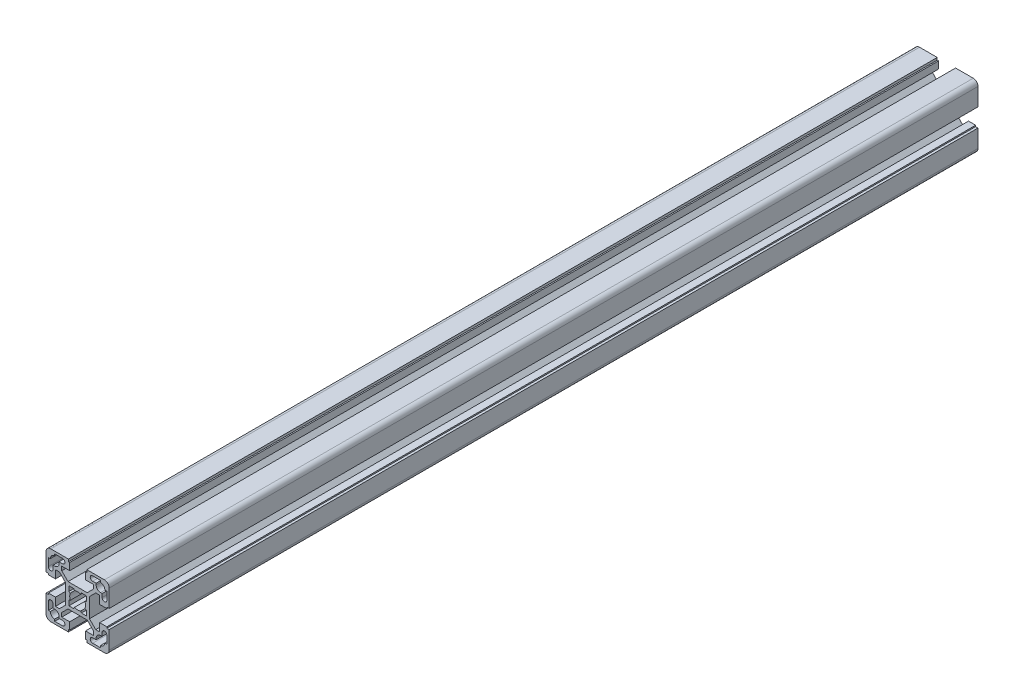
SolidWorks part; units mm, degrees
material "6061 Alloy"
ref_plane "Front Plane" through (0, 0, 0) normal (0, 0, 1) x (1, 0, 0)
ref_plane "Top Plane" through (0, 0, 0) normal (0, 1, 0) x (1, 0, 0)
ref_plane "Right Plane" through (0, 0, 0) normal (1, 0, 0) x (0, 0, -1)
sketch "Sketch1" plane through (0, 0, 0) normal (0, 0, 1) x (1, 0, 0)
  line L0 (5.8, -20) -> (17, -20)
  line L1 (14, -10.05) -> (11.4642, -10.05)
  line L2 (0, -21.1722) -> (0, 18.817) construction
  line L3 (0, 21.1722) -> (0, -18.817) construction
  line L4 (14.5, -18.5) -> (9.5, -18.5)
  line L5 (18.5, 5) -> (14, 5)
  line L6 (6.0858, -7.5) -> (10.05, -11.4642)
  line L7 (20, 5.8) -> (18.5, 5.8)
  line L8 (14, 5) -> (14, 10.05)
  line L9 (18.5, 5.8) -> (18.5, 5)
  line L10 (18.5, 14.5) -> (17.25, 14.5)
  line L11 (14.5, 11.75) -> (15.5, 11.75)
  line L12 (14.5, 17.25) -> (14.5, 18.5)
  line L13 (18.5, 9.5) -> (18.5, 14.5)
  line L14 (15.5, 11.75) -> (15.5, 9.5)
  line L15 (20, 17) -> (20, 5.8)
  line L16 (5.5, 5.5) -> (2.3979, 5.5)
  line L17 (2.3979, 5.5) -> (1.9983, 4.5833)
  line L18 (5.5, 2.3979) -> (5.5, 5.5)
  line L19 (4.5833, 1.9983) -> (5.5, 2.3979)
  line L20 (5, -14) -> (5, -18.5)
  line L21 (11.4642, 10.05) -> (7.5, 6.0858)
  line L22 (-6.0858, 7.5) -> (6.0858, 7.5)
  line L23 (11.75, 15.5) -> (11.75, 14.5)
  line L24 (5, -18.5) -> (5.8, -18.5)
  line L25 (5.8, -18.5) -> (5.8, -20)
  line L26 (10.05, -11.4642) -> (10.05, -14)
  line L27 (10.05, -14) -> (5, -14)
  line L28 (9.5, -15.5) -> (11.75, -15.5)
  line L29 (11.75, -15.5) -> (11.75, -14.5)
  line L30 (9.5, 15.5) -> (11.75, 15.5)
  line L31 (10.05, 14) -> (5, 14)
  line L32 (10.05, 11.4642) -> (10.05, 14)
  line L33 (5.8, 18.5) -> (5.8, 20)
  line L34 (5, 18.5) -> (5.8, 18.5)
  line L35 (7.5, -6.0858) -> (7.5, 6.0858)
  line L36 (5, 14) -> (5, 18.5)
  line L37 (6.0858, 7.5) -> (10.05, 11.4642)
  line L38 (14.5, 18.5) -> (9.5, 18.5)
  line L39 (14, 10.05) -> (11.4642, 10.05)
  line L40 (5.8, 20) -> (17, 20)
  line L41 (-18.5, -5) -> (-14, -5)
  line L42 (-6.0858, -7.5) -> (6.0858, -7.5)
  line L43 (11.4642, -10.05) -> (7.5, -6.0858)
  line L44 (-20, -5.8) -> (-18.5, -5.8)
  line L45 (-14, -5) -> (-14, -10.05)
  line L46 (-18.5, -5.8) -> (-18.5, -5)
  line L47 (-18.5, -14.5) -> (-17.25, -14.5)
  line L48 (4.5833, -1.9983) -> (5.5, -2.3979)
  line L49 (5.5, -2.3979) -> (5.5, -5.5)
  line L50 (2.3979, -5.5) -> (1.9983, -4.5833)
  line L51 (5.5, -5.5) -> (2.3979, -5.5)
  line L52 (-14.5, -11.75) -> (-15.5, -11.75)
  line L53 (-14.5, -17.25) -> (-14.5, -18.5)
  line L54 (-18.5, -9.5) -> (-18.5, -14.5)
  line L55 (-15.5, -11.75) -> (-15.5, -9.5)
  line L56 (-20, -17) -> (-20, -5.8)
  line L57 (-5.5, -5.5) -> (-2.3979, -5.5)
  line L58 (-2.3979, -5.5) -> (-1.9983, -4.5833)
  line L59 (-5.5, -2.3979) -> (-5.5, -5.5)
  line L60 (-4.5833, -1.9983) -> (-5.5, -2.3979)
  line L61 (-11.4642, -10.05) -> (-7.5, -6.0858)
  line L62 (-5.8, 20) -> (-17, 20)
  line L63 (-14, 10.05) -> (-11.4642, 10.05)
  line L64 (-14.5, 18.5) -> (-9.5, 18.5)
  line L65 (-6.0858, 7.5) -> (-10.05, 11.4642)
  line L66 (-5, 14) -> (-5, 18.5)
  line L67 (-7.5, -6.0858) -> (-7.5, 6.0858)
  line L68 (-5, 18.5) -> (-5.8, 18.5)
  line L69 (-5.8, 18.5) -> (-5.8, 20)
  line L70 (-10.05, 11.4642) -> (-10.05, 14)
  line L71 (-10.05, 14) -> (-5, 14)
  line L72 (-9.5, 15.5) -> (-11.75, 15.5)
  line L73 (-11.75, -15.5) -> (-11.75, -14.5)
  line L74 (-9.5, -15.5) -> (-11.75, -15.5)
  line L75 (-10.05, -14) -> (-5, -14)
  line L76 (-10.05, -11.4642) -> (-10.05, -14)
  line L77 (-5.8, -18.5) -> (-5.8, -20)
  line L78 (-5, -18.5) -> (-5.8, -18.5)
  line L79 (-11.75, 15.5) -> (-11.75, 14.5)
  line L80 (-11.4642, 10.05) -> (-7.5, 6.0858)
  line L81 (-5, -14) -> (-5, -18.5)
  line L82 (-4.5833, 1.9983) -> (-5.5, 2.3979)
  line L83 (-5.5, 2.3979) -> (-5.5, 5.5)
  line L84 (-2.3979, 5.5) -> (-1.9983, 4.5833)
  line L85 (-5.5, 5.5) -> (-2.3979, 5.5)
  line L86 (-20, 17) -> (-20, 5.8)
  line L87 (-15.5, 11.75) -> (-15.5, 9.5)
  line L88 (20, -17) -> (20, -5.8)
  line L89 (15.5, -11.75) -> (15.5, -9.5)
  line L90 (18.5, -9.5) -> (18.5, -14.5)
  line L91 (14.5, -17.25) -> (14.5, -18.5)
  line L92 (14.5, -11.75) -> (15.5, -11.75)
  line L93 (18.5, -14.5) -> (17.25, -14.5)
  line L94 (-18.5, 9.5) -> (-18.5, 14.5)
  line L95 (-14.5, 17.25) -> (-14.5, 18.5)
  line L96 (18.5, -5.8) -> (18.5, -5)
  line L97 (14, -5) -> (14, -10.05)
  line L98 (20, -5.8) -> (18.5, -5.8)
  line L99 (18.5, -5) -> (14, -5)
  line L100 (-14.5, 11.75) -> (-15.5, 11.75)
  line L101 (-18.5, 14.5) -> (-17.25, 14.5)
  line L102 (-18.5, 5.8) -> (-18.5, 5)
  line L103 (-14, 5) -> (-14, 10.05)
  line L104 (-20, 5.8) -> (-18.5, 5.8)
  line L105 (-6.0858, -7.5) -> (-10.05, -11.4642)
  line L106 (-18.5, 5) -> (-14, 5)
  line L107 (-14.5, -18.5) -> (-9.5, -18.5)
  line L108 (-20, 0) -> (20.788, 0) construction
  line L109 (-14, -10.05) -> (-11.4642, -10.05)
  line L110 (-5.8, -20) -> (-17, -20)
  arc A0 (14.5, -11.75) -> (11.75, -14.5) centre (14.5, -14.5) ccw
  arc A1 (18.5, 9.5) -> (15.5, 9.5) centre (17, 9.5) cw
  arc A2 (14.5, 17.25) -> (17.25, 14.5) centre (14.5, 14.5) cw
  arc A3 (17, 20) -> (20, 17) centre (17, 17) cw
  arc A4 (-1.9983, 4.5833) -> (1.9983, 4.5833) centre (0, 0) cw
  arc A5 (9.5, 15.5) -> (9.5, 18.5) centre (9.5, 17) cw
  arc A6 (9.5, -15.5) -> (9.5, -18.5) centre (9.5, -17) ccw
  arc A7 (14.5, 11.75) -> (11.75, 14.5) centre (14.5, 14.5) cw
  arc A8 (4.5833, -1.9983) -> (4.5833, 1.9983) centre (0, 0) ccw
  arc A9 (-18.5, -9.5) -> (-15.5, -9.5) centre (-17, -9.5) cw
  arc A10 (-14.5, -17.25) -> (-17.25, -14.5) centre (-14.5, -14.5) cw
  arc A11 (-1.9983, -4.5833) -> (1.9983, -4.5833) centre (0, 0) ccw
  arc A12 (-17, -20) -> (-20, -17) centre (-17, -17) cw
  arc A13 (-4.5833, -1.9983) -> (-4.5833, 1.9983) centre (0, 0) cw
  arc A14 (-14.5, 11.75) -> (-11.75, 14.5) centre (-14.5, 14.5) ccw
  arc A15 (-9.5, -15.5) -> (-9.5, -18.5) centre (-9.5, -17) cw
  arc A16 (-9.5, 15.5) -> (-9.5, 18.5) centre (-9.5, 17) ccw
  arc A17 (-17, 20) -> (-20, 17) centre (-17, 17) ccw
  arc A18 (17, -20) -> (20, -17) centre (17, -17) ccw
  arc A19 (14.5, -17.25) -> (17.25, -14.5) centre (14.5, -14.5) ccw
  arc A20 (18.5, -9.5) -> (15.5, -9.5) centre (17, -9.5) ccw
  arc A21 (-14.5, 17.25) -> (-17.25, 14.5) centre (-14.5, 14.5) ccw
  arc A22 (-18.5, 9.5) -> (-15.5, 9.5) centre (-17, 9.5) ccw
  arc A23 (-14.5, -11.75) -> (-11.75, -14.5) centre (-14.5, -14.5) cw
  point P55 (7.5, 0)
  point P101 (-7.5, 0)
  point P116 (0, -7.5)
  point P149 (0, 7.5)
extrude "Extrude1" add sketch "Sketch1" along normal mid plane 550
hole_wizard "M12 Tapped Hole1" positions "3DSketch2" profile "Sketch3" tap size "M12" standard "ISO"
sketch3d "3DSketch2"
  line L0 (-20, 17, 0) -> (-20, 5.8, 0) construction
  line L1 (-5.8, 20, 0) -> (-17, 20, 0) construction
  line L2 (-5.8, 20, 200) -> (-17, 20, 200) construction
  line L3 (-20, 17, 200) -> (-20, 5.8, 200) construction
  point P0 (0, 0, 200)
  point P2 (0, 0, 0)
  dimension "D1" = 20
  dimension "D2" = 20
  dimension "D3" = 20
  dimension "D4" = 20
sketch "Sketch3" plane through (0, 0, 200) normal (1, 0, 0) x (0, -1, 0)
  line L0 (0, 0) -> (0, 35.8144)
  line L1 (0, 35.8144) -> (5.1, 32.75)
  line L2 (5.1, 32.75) -> (5.1, 0.925)
  line L3 (5.1, 0.925) -> (6.025, 0)
  line L5 (6.025, 0) -> (0, 0)
  line L6 (-5.1, 0.925) -> (-6.025, 0) construction
  line L10 (0, 35.8144) -> (-5.1, 32.75) construction
  line L11 (0, -6.35) -> (0, 107.95) construction
  dimension "Tap Drill Dia." = 10.2
  dimension "Tap Drill Depth" = 32.75
  dimension "Near C'Sink Dia." = 12.05
  dimension "Near C'Sink Angle" = 90
  dimension "Drill Angle" = 118
cosmetic thread "Hole Thread1" [suppressed] parameters "D1"=24, "D2"=12
cosmetic thread "Hole Thread2" [suppressed] parameters "D1"=24, "D2"=12
hole_wizard "Ø9.8 (9.8) Diameter Hole1" positions "3DSketch3" profile "Sketch4" hole size "Ø9.8" standard "ISO"
sketch3d "3DSketch3"
  line L0 (-5.8, 20, 200) -> (-17, 20, 200) construction
  line L1 (20, -17, 200) -> (20, -5.8, 200) construction
  line L2 (17, 20, 0) -> (5.8, 20, 0) construction
  line L3 (20, -17, 0) -> (20, -5.8, 0) construction
  point P0 (0, 20, 184)
  point P2 (20, 0, 184)
  point P4 (0, 20, 16)
  point P6 (20, 0, 16)
  dimension "D1" = 16
  dimension "D2" = 20
  dimension "D3" = 20
  dimension "D4" = 16
  dimension "D5" = 16
  dimension "D6" = 16
sketch "Sketch4" plane through (0, 20, 184) normal (1, 0, 0) x (0, 0, 1)
  line L0 (0, 0) -> (0, 40)
  line L1 (0, 40) -> (4.9, 40)
  line L2 (4.9, 40) -> (4.9, 0)
  line L5 (4.9, 0) -> (0, 0)
  line L11 (0, -6.35) -> (0, 107.95) construction
  dimension "Thru Hole Dia." = 9.8
  dimension "Thru Hole Depth" = 40
hole_wizard "Ø17.0 (17) Diameter Hole1" positions "3DSketch4" profile "Sketch5" hole size "Ø17.0" standard "ISO"
sketch3d "3DSketch4"
  line L0 (-5.8, 20, 200) -> (-17, 20, 200) construction
  line L1 (-5.8, 20, 0) -> (-17, 20, 0) construction
  point P0 (0, 20, 177.5)
  point P2 (0, 20, 22.5)
  dimension "D1" = 20
  dimension "D2" = 22.5
  dimension "D3" = 22.5
sketch "Sketch5" plane through (0, 20, 177.5) normal (1, 0, 0) x (0, 0, 1)
  line L0 (0, 0) -> (0, 40)
  line L1 (0, 40) -> (8.5, 40)
  line L2 (8.5, 40) -> (8.5, 0)
  line L5 (8.5, 0) -> (0, 0)
  line L11 (0, -6.35) -> (0, 107.95) construction
  dimension "Thru Hole Dia." = 17
  dimension "Thru Hole Depth" = 40
